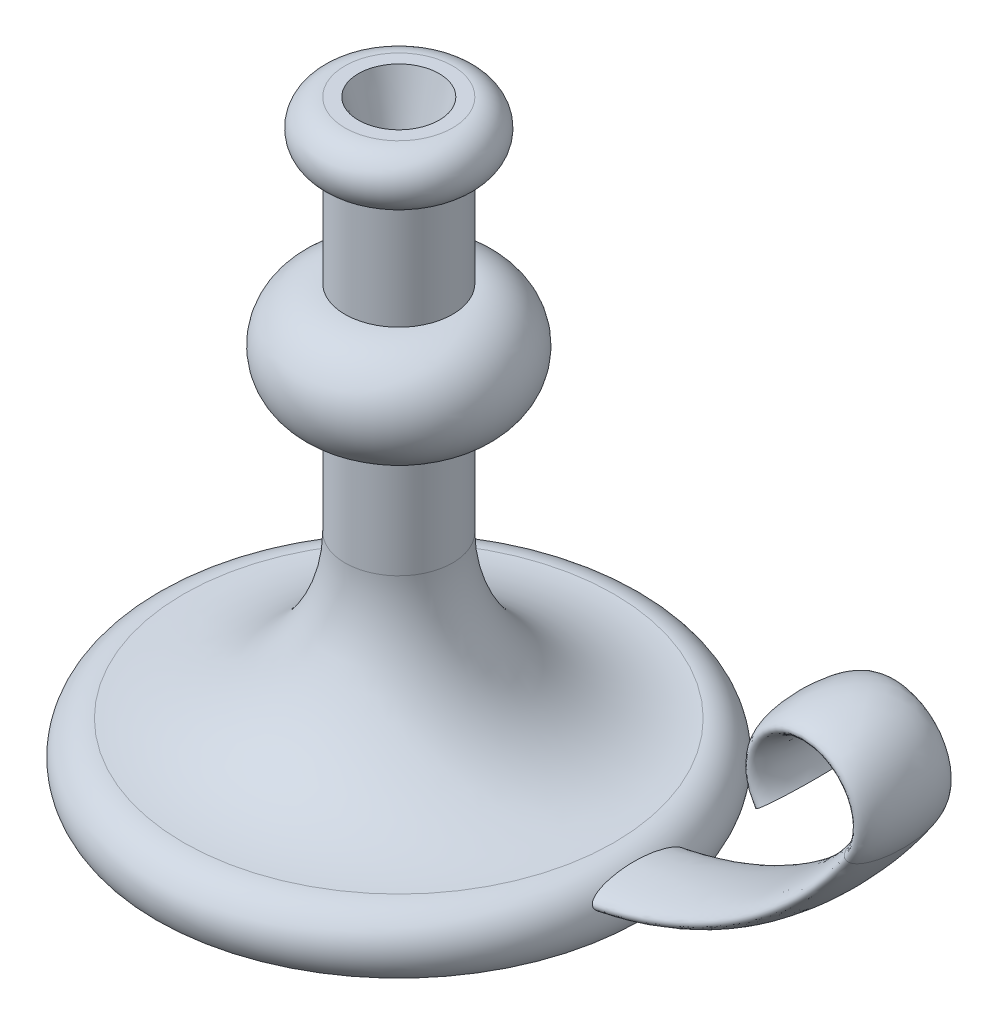
SolidWorks part; units mm, degrees
ref_plane "Front" through (0, 0, 0) normal (0, 0, 1) x (1, 0, 0)
ref_plane "Top" through (0, 0, 0) normal (0, 1, 0) x (1, 0, 0)
ref_plane "Right" through (0, 0, 0) normal (1, 0, 0) x (0, 0, -1)
sketch "Sketch1" plane through (0, 0, 0) normal (0, 0, 1) x (1, 0, 0)
  line L0 (0, 0) -> (0, 220)
  line L1 (0, 220) -> (20, 220)
  line L2 (0, 0) -> (90, 0)
  line L3 (20, 200) -> (20, 160)
  line L4 (20, 120) -> (20, 80)
  arc A0 (20, 220) -> (20, 200) centre (20, 210) cw
  arc A1 (20, 160) -> (20, 120) centre (20, 140) cw
  arc A2 (20, 80) -> (80, 20) centre (80, 80) ccw
  arc A3 (80, 20) -> (90, 0) centre (80, 7.5) cw
  dimension "D4" = 10
  dimension "D5" = 20
  dimension "D2" = 60
  dimension "D3" = 12.5
  dimension "D1" = 20
  dimension "D6" = 40
  dimension "D7" = 220
  dimension "D8" = 80
  dimension "D9" = 90
revolve "Revolve1" add sketch "Sketch1" angle 360 about L0
sketch "Sketch2" plane through (0, 0, 0) normal (0, 0, 1) x (1, 0, 0)
  line L0 (0, 10) -> (60, 10)
  line L1 (0, 160) -> (0, 200) construction
  line L2 (-90, 0) -> (90, 0) construction
  arc A0 (60, 10) -> (183.5921, 75) centre (60, 160) ccw
  arc A1 (183.5921, 75) -> (150.6342, 75) centre (167.1131, 86.3333) ccw
  dimension "D2" = 150
  dimension "D4" = 20
  dimension "D1" = 60
  dimension "D3" = 65
  dimension "D5" = 10
sketch "Sketch3" plane through (0, 0, 0) normal (1, 0, 0) x (0, 0, -1)
  ellipse E0 centre (0, 10) end of major axis (17.5, 10) minor radius 5
  dimension "D1" = 35
  dimension "D2" = 10
sweep "Sweep1" add profiles "Sketch3" path "Sketch2"
sketch "Sketch4" plane through (0, 220, 0) normal (0, 1, 0) x (1, 0, 0)
  circle A0 centre (0, 0) radius 15
  dimension "D1" = 30
extrude "Cut-Extrude1" cut sketch "Sketch4" against normal blind 25 draft 15
